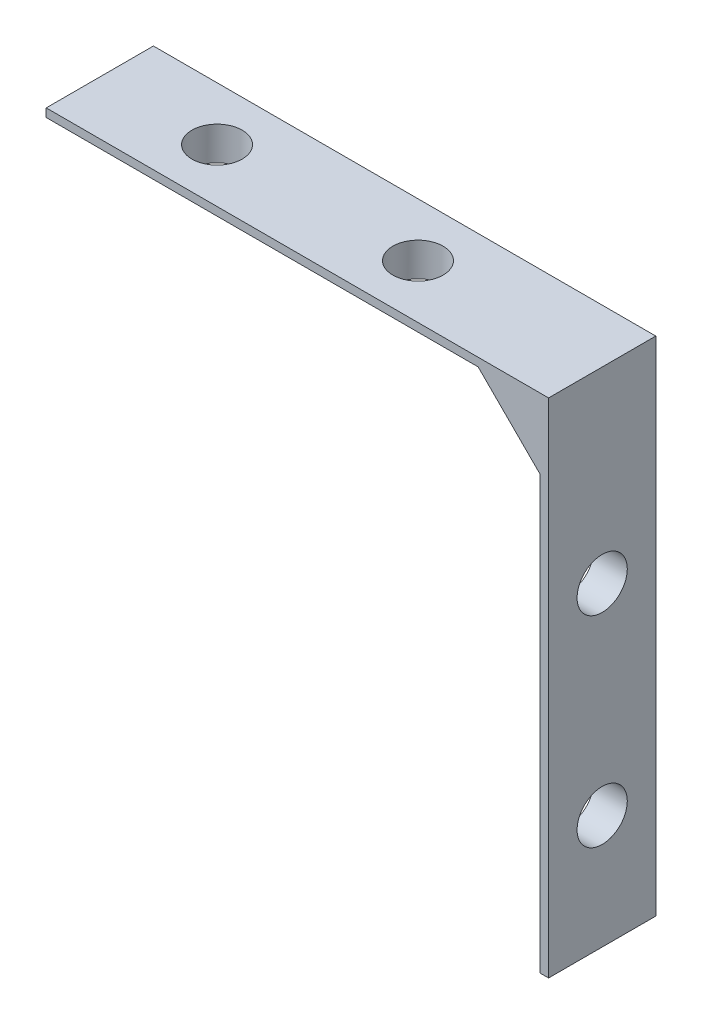
SolidWorks part; units mm, degrees
ref_plane "Front Plane" through (0, 0, 0) normal (0, 0, 1) x (1, 0, 0)
ref_plane "Top Plane" through (0, 0, 0) normal (0, 1, 0) x (1, 0, 0)
ref_plane "Right Plane" through (0, 0, 0) normal (1, 0, 0) x (0, 0, -1)
sketch "Sketch1" plane through (0, 0, 0) normal (0, 0, 1) x (1, 0, 0)
  line L1 (-4.8284, -2) -> (-2, -4.8284)
  line L2 (0, 0) -> (-30, 0)
  line L3 (0, 0) -> (0, -2)
  line L5 (-30, 0) -> (-30, -2)
  line L7 (0, -2) -> (0, -30)
  line L8 (0, -30) -> (-2, -30)
  line L9 (-2, -4.8284) -> (-2, -30)
  line L10 (-4.8284, -2) -> (-30, -2)
  dimension "D1" = 30
  dimension "D2" = 2
  dimension "D3" = 2
  dimension "D4" = 28
  dimension "D5" = 4
extrude "Boss-Extrude1" add sketch "Sketch1" along normal blind 6.4
sketch "Sketch2" plane through (0, 0, 0) normal (0, 1, 0) x (1, 0, 0)
  line L0 (-30, -6.4) -> (-30, 0) construction
  line L4 (0, 0) -> (-30, 0) construction
  circle A0 centre (-23, -3.2) radius 1.5
  circle A1 centre (-11, -3.2) radius 1.5
  dimension "D1" = 3
  dimension "D2" = 3
  dimension "D3" = 12
  dimension "D4" = 7
  dimension "D6" = 3.2
extrude "Cut-Extrude1" cut sketch "Sketch2" against normal up to surface (2 mm away) up to face at (-17.4142, -2, 3.2)
sketch "Sketch3" plane through (0, 0, 0) normal (1, 0, 0) x (0, 0, -1)
  line L2 (-6.4, 0) -> (0, 0) construction
  circle A0 centre (-3.2, -11.1937) radius 1.5
  circle A1 centre (-3.2, -23.1937) radius 1.5
  dimension "D1" = 3
  dimension "D2" = 3
  dimension "D4" = 12
  dimension "D6" = 11.1937
  dimension "D3" = 3.2
extrude "Cut-Extrude2" cut sketch "Sketch3" against normal up to surface (2 mm away) up to face at (-2, -17.4142, 3.2)
chamfer "Chamfer9" distance 1.5 angle 45 1 edges at (-17.4142, -2, 0)
chamfer "Chamfer10" distance 1.5 angle 45 2 edges at (-2, -17.4142, 0) (-4.1642, -2.6642, 0)
chamfer "Chamfer11" distance 1.5 angle 45 3 edges at (-2, -17.4142, 6.4) (-3.4142, -3.4142, 6.4) (-17.4142, -2, 6.4)
